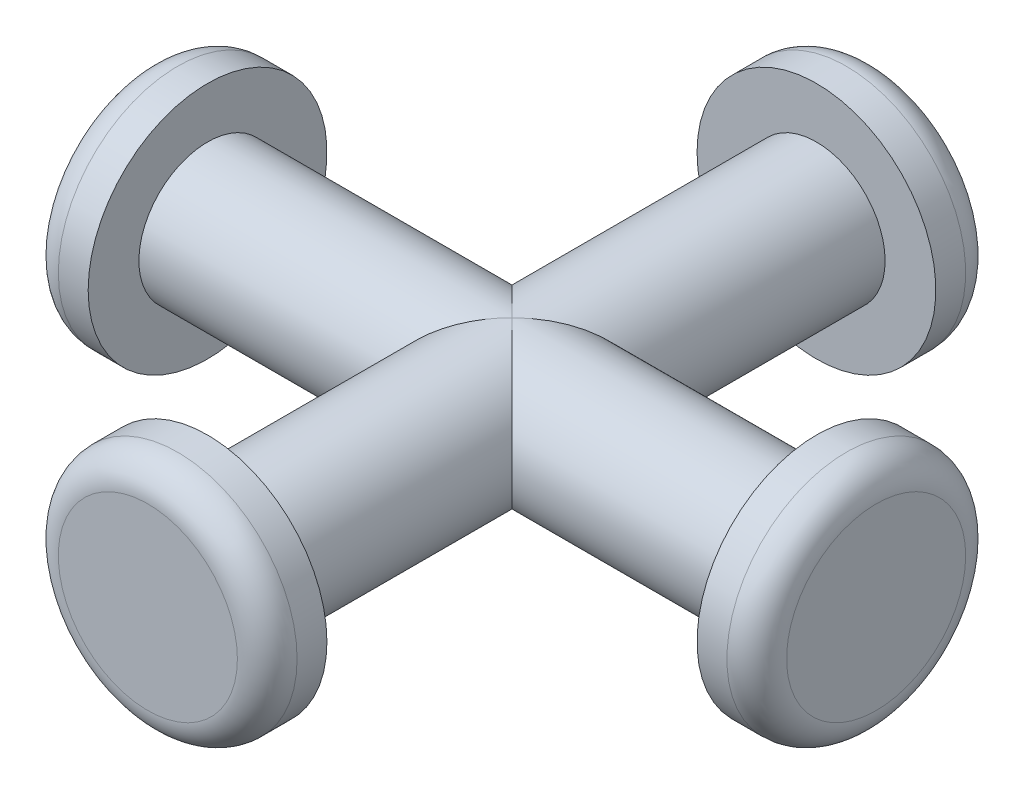
SolidWorks part; units mm, degrees
ref_plane "Plan de face" through (0, 0, 0) normal (0, 0, 1) x (1, 0, 0)
ref_plane "Plan de dessus" through (0, 0, 0) normal (0, 1, 0) x (1, 0, 0)
ref_plane "Plan de droite" through (0, 0, 0) normal (1, 0, 0) x (0, 0, -1)
sketch "Esquisse1" plane through (0, 0, 0) normal (0, 0, 1) x (1, 0, 0)
  circle A0 centre (0, 0) radius 2.3
  dimension "D1" = 4.6
extrude "Boss.-Extru.1" add sketch "Esquisse1" along normal mid plane 20.4 contours A0
sketch "Esquisse3" plane through (0, 0, 0) normal (1, 0, 0) x (0, 0, -1)
  circle A0 centre (0, 0) radius 2.3
  dimension "D1" = 4.6
extrude "Boss.-Extru.2" add sketch "Esquisse3" along normal mid plane 20.4
sketch "Esquisse4" plane through (10.2, 0, 0) normal (1, 0, 0) x (0, 0, -1)
  circle A0 centre (0, 0) radius 4
  dimension "D1" = 8
extrude "Boss.-Extru.3" add sketch "Esquisse4" along normal blind 2 contours A0
sketch "Esquisse5" plane through (-10.2, 0, 0) normal (-1, 0, 0) x (0, 0, 1)
  circle A0 centre (0, 0) radius 4
  dimension "D1" = 8
extrude "Boss.-Extru.4" add sketch "Esquisse5" along normal blind 2
sketch "Esquisse6" plane through (0, 0, 10.2) normal (0, 0, 1) x (1, 0, 0)
  circle A0 centre (0, 0) radius 4
  dimension "D1" = 8
extrude "Boss.-Extru.5" add sketch "Esquisse6" along normal blind 2
sketch "Esquisse7" plane through (0, 0, -10.2) normal (0, 0, -1) x (-1, 0, 0)
  circle A0 centre (0, 0) radius 4
  dimension "D1" = 8
extrude "Boss.-Extru.6" add sketch "Esquisse7" along normal blind 2 contours A0
fillet "Congé1" radius 1 4 edges at (-12.2, 0, 4) (-4, 0, -12.2) (12.2, 0, -4) (4, 0, 12.2)
